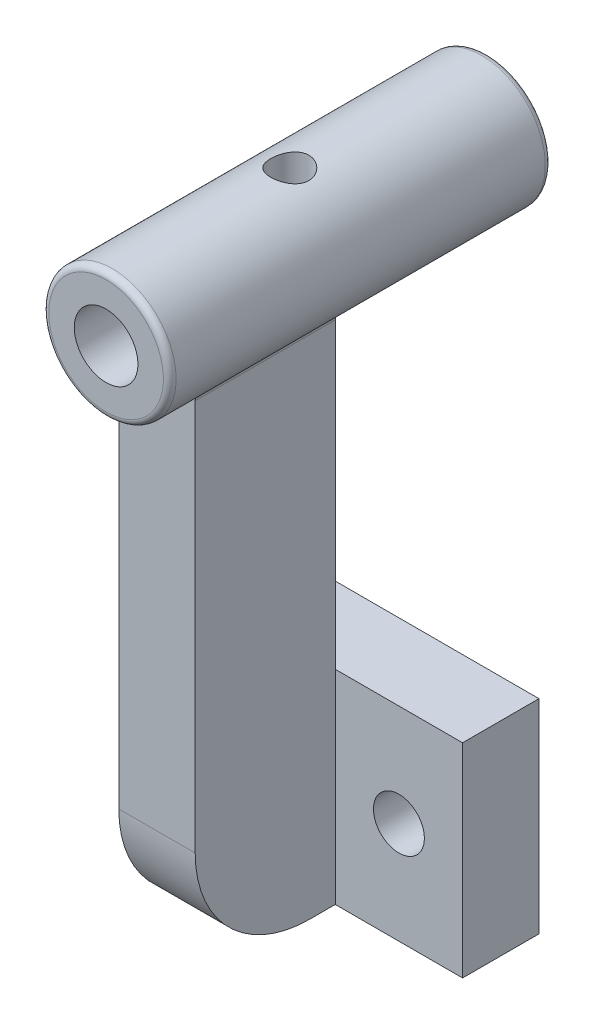
SolidWorks part; units mm, degrees
material "Brass"
ref_plane "Front Plane" through (0, 0, 0) normal (0, 0, 1) x (1, 0, 0)
ref_plane "Top Plane" through (0, 0, 0) normal (0, 1, 0) x (1, 0, 0)
ref_plane "Right Plane" through (0, 0, 0) normal (1, 0, 0) x (0, 0, -1)
sketch "Sketch2" plane through (0, 0, 0) normal (0, 0, 1) x (1, 0, 0)
  line L1 (0, 0) -> (13, 0)
  line L2 (0, 0) -> (0, 16)
  line L3 (0, 16) -> (13, 16)
  line L4 (13, 0) -> (13, 16)
  line L5 (13, 16) -> (-13, 16)
  line L6 (13, 16) -> (13, 0)
  line L7 (13, 0) -> (-13, 0)
  line L8 (-13, 16) -> (-13, 0)
  circle A0 centre (-8, 8) radius 2
  circle A1 centre (8, 8) radius 2
  dimension "D4" = 8
  dimension "D1" = 16
  dimension "D2" = 13
  dimension "D3" = 26
  dimension "D5" = 8
  dimension "D6" = 5
  dimension "D7" = 16
extrude "Boss-Extrude1" add sketch "Sketch2" along normal blind 6 contours L5 L8 L7 L2 A0 | L1 L4 L3 L2 A1
sketch "Sketch3" plane through (0, 0, 0) normal (1, 0, 0) x (0, 0, -1)
  line L0 (-6, 0) -> (-8, 0)
  line L1 (-17, 9) -> (-17, 44)
  line L2 (-17, 44) -> (-6, 44)
  line L3 (-6, 44) -> (-6, 16)
  line L4 (-6, 0) -> (-6, 16)
  arc A0 (-8, 0) -> (-17, 9) centre (-8, 9) cw
  point P10 (-17, 0)
  dimension "D3" = 9
  dimension "D1" = 11
  dimension "D2" = 44
extrude "Boss-Extrude2" add sketch "Sketch3" along normal blind 3 and the other way blind 3
sketch "Sketch6" plane through (0, 0, 6) normal (0, 0, -1) x (-1, 0, 0)
  line L0 (3, 44) -> (-3, 44) construction
  circle A0 centre (0, 44) radius 5
extrude "Boss-Extrude4" add sketch "Sketch6" along normal blind 15 and the other way blind 15
sketch "Sketch7" plane through (0, 0, -9) normal (0, 0, -1) x (-1, 0, 0)
  circle A0 centre (0, 44) radius 2.5
extrude "Cut-Extrude2" cut sketch "Sketch7" against normal through all
fillet "Fillet3" radius 0.5 2 edges at (-5, 44, 21) (-5, 44, -9)
fillet "Fillet4" radius 0.5 2 edges at (-3, 40, 11.5) (3, 40, 11.5)
sketch "Sketch8" plane through (0, 0, 0) normal (1, 0, 0) x (0, 0, -1)
  line L0 (-6, 38.0701) -> (-6, 50.5304) construction
  line L1 (-6, 16) -> (-6, 39.7574) construction
sketch "Sketch9" plane through (0, 0, 0) normal (1, 0, 0) x (0, 0, -1)
  line L0 (8.4301, 49) -> (-20.5, 49)
  line L1 (8.5, 49) -> (-20.5, 49) construction
ref_plane "Plane1" through (0, 49, 0) normal (0, 1, 0) x (0, 0, 1)
sketch "Sketch10" plane through (0, 49, 0) normal (0, 1, 0) x (0, 0, 1)
  line L0 (-8.4301, 0) -> (6.5699, 0)
  line L1 (-8.4301, 0) -> (20.5, 0) construction
  circle A0 centre (6.5699, 0) radius 1.5
  dimension "D1" = 15
extrude "Cut-Extrude3" cut sketch "Sketch10" against normal blind 4
